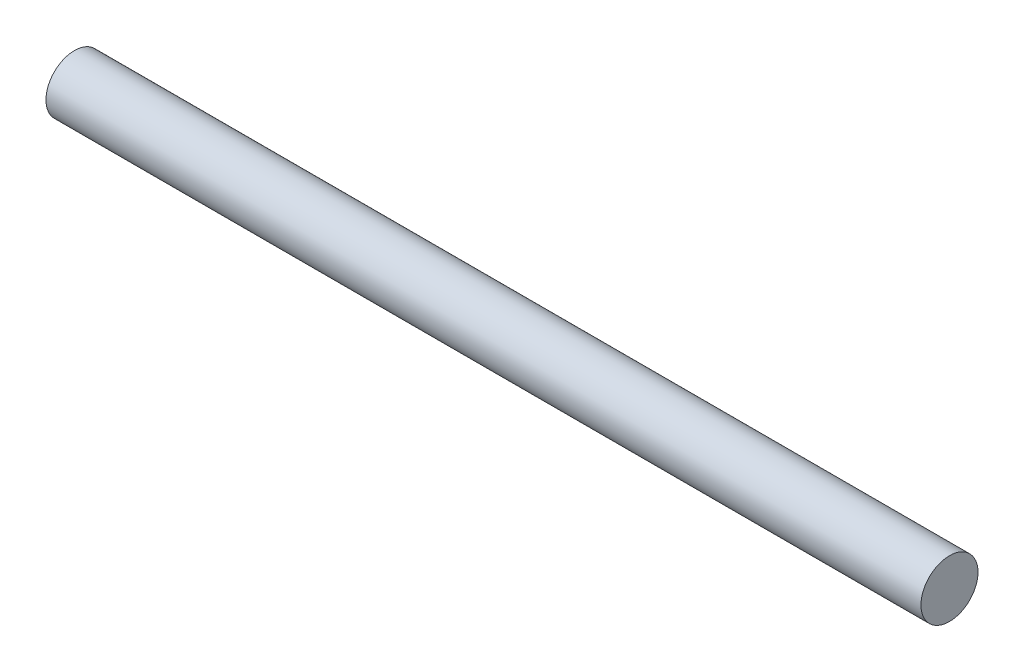
SolidWorks part; units mm, degrees
ref_plane "Front Plane" through (0, 0, 0) normal (0, 0, 1) x (1, 0, 0)
ref_plane "Top Plane" through (0, 0, 0) normal (0, 1, 0) x (1, 0, 0)
ref_plane "Right Plane" through (0, 0, 0) normal (1, 0, 0) x (0, 0, -1)
sketch "Sketch1" plane through (0, 0, 0) normal (1, 0, 0) x (0, 0, -1)
  circle A0 centre (0, 0) radius 2.286
extrude "Boss-Extrude1" add sketch "Sketch1" along normal blind 70.104
equation "\"rodDiameter\"=0.18"
equation "\"protectorBoxRodLength\"=2.76"
equation "\"D1@Boss-Extrude1\"=\"protectorBoxRodLength\""
